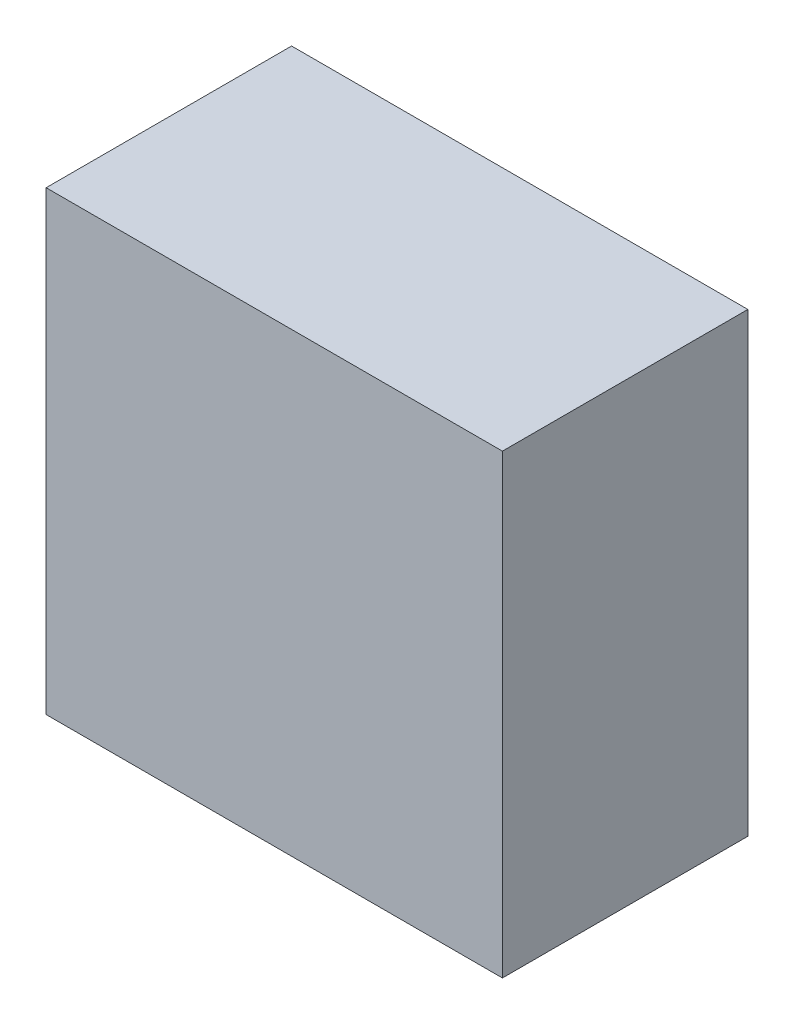
SolidWorks part; units mm, degrees
material "Pine"
ref_plane "Front Plane" through (0, 0, 0) normal (0, 0, 1) x (1, 0, 0)
ref_plane "Top Plane" through (0, 0, 0) normal (0, 1, 0) x (1, 0, 0)
ref_plane "Right Plane" through (0, 0, 0) normal (1, 0, 0) x (0, 0, -1)
sketch "Sketch1" plane through (0, 0, 0) normal (0, 0, 1) x (1, 0, 0)
  line L1 (600, 72.5) -> (455, 72.5)
  line L2 (600, 72.5) -> (600, -72.5)
  line L3 (600, -72.5) -> (455, -72.5)
  line L4 (455, 72.5) -> (455, -72.5)
  dimension "D1" = 145
  dimension "D2" = 145
extrude "Boss-Extrude1" add sketch "Sketch1" along normal blind 78
